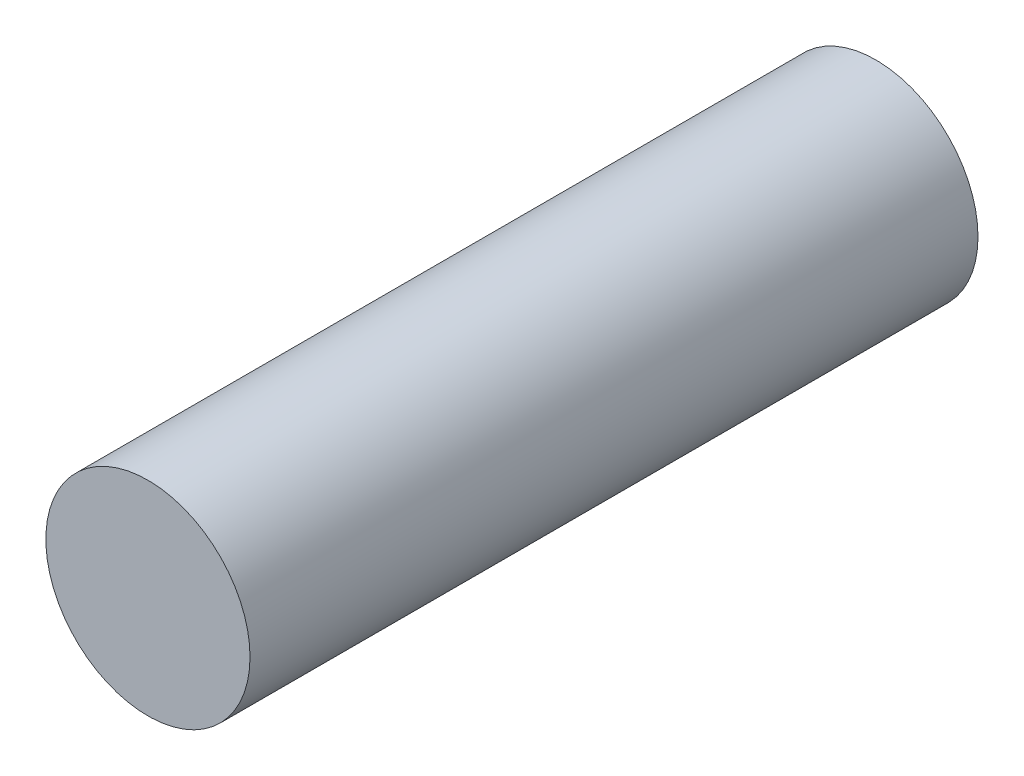
SolidWorks part; units mm, degrees
material "6061-T6 (SS)"
ref_plane "Front Plane" through (0, 0, 0) normal (0, 0, 1) x (1, 0, 0)
ref_plane "Top Plane" through (0, 0, 0) normal (0, 1, 0) x (1, 0, 0)
ref_plane "Right Plane" through (0, 0, 0) normal (1, 0, 0) x (0, 0, -1)
sketch "Sketch1" plane through (0, 0, 0) normal (0, 0, 1) x (1, 0, 0)
  circle A0 centre (0, 0) radius 18.2563
  dimension "D1" = 36.5125
extrude "Boss-Extrude1" add sketch "Sketch1" along normal mid plane 130.175
chamfer "Chamfer1" [suppressed] distance 25.4 distance2 3.9688
